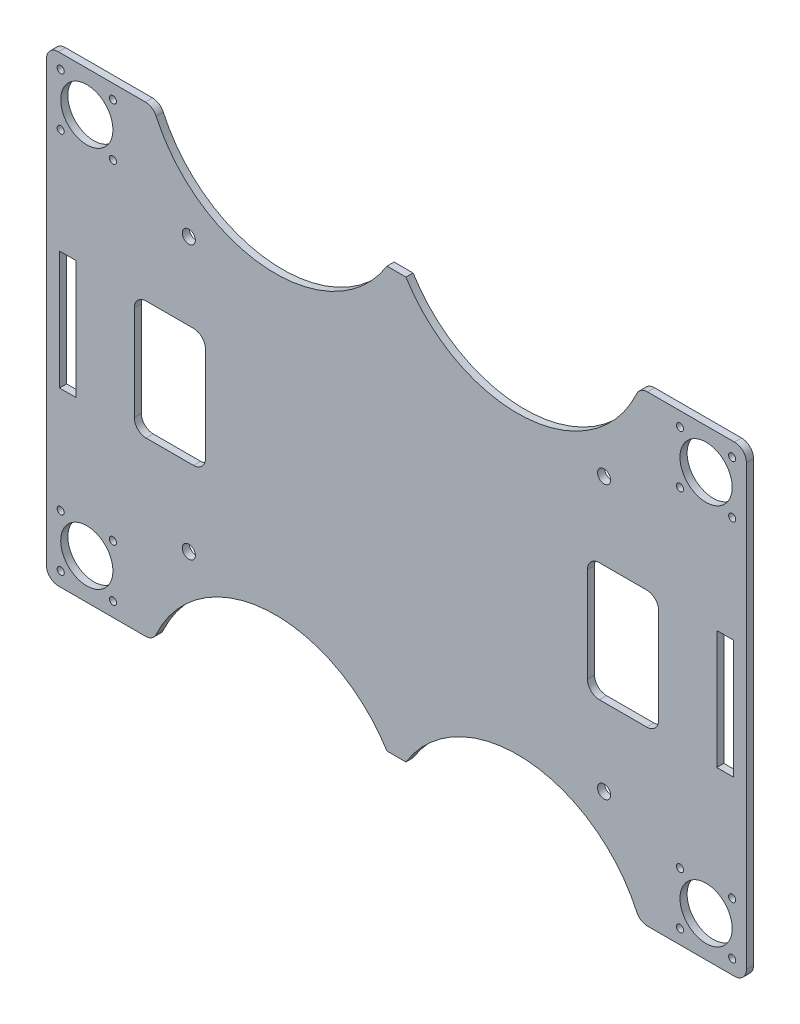
SolidWorks part; units mm, degrees
ref_plane "Plan de face" through (0, 0, 0) normal (0, 0, 1) x (1, 0, 0)
ref_plane "Plan de dessus" through (0, 0, 0) normal (0, 1, 0) x (1, 0, 0)
ref_plane "Plan de droite" through (0, 0, 0) normal (1, 0, 0) x (0, 0, -1)
sketch "Esquisse1" plane through (0, 0, 0) normal (0, 0, 1) x (1, 0, 0)
  line L0 (147.5, 48.0502) -> (147.5, -224.4935) construction
  line L1 (5, 0) -> (41.6849, 0)
  line L2 (0, -5) -> (0, -190)
  line L3 (5, -195) -> (41.6849, -195)
  line L4 (295, -5) -> (295, -190)
  line L5 (-64.1158, -97.5) -> (352.9454, -97.5) construction
  line L6 (253.3151, 0) -> (290, 0)
  line L7 (253.3151, -195) -> (290, -195)
  line L8 (151.5, -9) -> (143.5, -9)
  line L9 (151.5, -186) -> (143.5, -186)
  line L10 (-26.8235, -17) -> (37.1508, -17) construction
  line L11 (17, 13.3483) -> (17, -39.4559) construction
  line L12 (-23.9724, 20) -> (312.0368, 20) construction
  line L13 (96.4886, 48.0502) -> (96.4886, 6.2328) construction
  line L14 (198.5114, 48.0502) -> (198.5114, 6.2328) construction
  line L15 (278, 13.3483) -> (278, -39.4559) construction
  line L16 (321.8235, -17) -> (257.8492, -17) construction
  line L17 (278, -208.3483) -> (278, -155.5441) construction
  line L18 (321.8235, -178) -> (257.8492, -178) construction
  line L19 (17, -208.3483) -> (17, -155.5441) construction
  line L20 (-26.8235, -178) -> (37.1508, -178) construction
  line L21 (228, -77.5) -> (228, -117.5)
  line L22 (42, -72.5) -> (62, -72.5)
  line L23 (37, -77.5) -> (37, -117.5)
  line L24 (42, -122.5) -> (62, -122.5)
  line L25 (67, -77.5) -> (67, -117.5)
  line L26 (253, -122.5) -> (233, -122.5)
  line L27 (258, -77.5) -> (258, -117.5)
  line L28 (253, -72.5) -> (233, -72.5)
  line L29 (289.5, -122.5) -> (282.5, -122.5)
  line L30 (5.5, -72.5) -> (12.5, -72.5)
  line L31 (5.5, -72.5) -> (5.5, -122.5)
  line L32 (5.5, -122.5) -> (12.5, -122.5)
  line L33 (12.5, -72.5) -> (12.5, -122.5)
  line L34 (289.5, -72.5) -> (282.5, -72.5)
  line L35 (289.5, -72.5) -> (289.5, -122.5)
  line L36 (282.5, -72.5) -> (282.5, -122.5)
  line L37 (9, -55.2244) -> (9, -136.6659) construction
  line L38 (52, -55.2244) -> (52, -136.6659) construction
  line L39 (243, -55.2244) -> (243, -136.6659) construction
  line L40 (286, -55.2244) -> (286, -136.6659) construction
  line L41 (236.6323, -55.75) -> (56.6881, -55.75) construction
  line L42 (236.6323, -139.25) -> (56.6881, -139.25) construction
  arc A0 (143.5, -9) -> (46.234, -2.9248) centre (96.4886, 20) cw
  arc A1 (151.5, -9) -> (248.766, -2.9248) centre (198.5114, 20) ccw
  arc A2 (151.5, -186) -> (248.766, -192.0752) centre (198.5114, -215) cw
  arc A3 (143.5, -186) -> (46.234, -192.0752) centre (96.4886, -215) ccw
  circle A4 centre (60, -40) radius 2.75
  circle A5 centre (17, -17) radius 11
  circle A6 centre (6, -6) radius 1.5
  circle A7 centre (28, -6) radius 1.5
  circle A8 centre (28, -28) radius 1.5
  circle A9 centre (6, -28) radius 1.5
  circle A10 centre (235, -40) radius 2.75
  circle A11 centre (289, -6) radius 1.5
  circle A12 centre (267, -6) radius 1.5
  circle A13 centre (278, -17) radius 11
  circle A14 centre (289, -28) radius 1.5
  circle A15 centre (267, -28) radius 1.5
  circle A16 centre (267, -189) radius 1.5
  circle A17 centre (289, -189) radius 1.5
  circle A18 centre (289, -167) radius 1.5
  circle A19 centre (267, -167) radius 1.5
  circle A20 centre (278, -178) radius 11
  circle A21 centre (235, -155) radius 2.75
  circle A22 centre (60, -155) radius 2.75
  circle A23 centre (6, -189) radius 1.5
  circle A24 centre (28, -189) radius 1.5
  circle A25 centre (17, -178) radius 11
  circle A26 centre (6, -167) radius 1.5
  circle A27 centre (28, -167) radius 1.5
  arc A28 (295, -5) -> (290, 0) centre (290, -5) ccw
  arc A29 (248.766, -2.9248) -> (253.3151, 0) centre (253.3151, -5) cw
  arc A30 (46.234, -2.9248) -> (41.6849, 0) centre (41.6849, -5) ccw
  arc A31 (5, 0) -> (0, -5) centre (5, -5) ccw
  arc A32 (0, -190) -> (5, -195) centre (5, -190) ccw
  arc A33 (41.6849, -195) -> (46.234, -192.0752) centre (41.6849, -190) ccw
  arc A34 (248.766, -192.0752) -> (253.3151, -195) centre (253.3151, -190) ccw
  arc A35 (290, -195) -> (295, -190) centre (290, -190) ccw
  arc A36 (42, -72.5) -> (37, -77.5) centre (42, -77.5) ccw
  arc A37 (37, -117.5) -> (42, -122.5) centre (42, -117.5) ccw
  arc A38 (62, -122.5) -> (67, -117.5) centre (62, -117.5) ccw
  arc A39 (67, -77.5) -> (62, -72.5) centre (62, -77.5) ccw
  arc A40 (233, -72.5) -> (228, -77.5) centre (233, -77.5) ccw
  arc A41 (228, -117.5) -> (233, -122.5) centre (233, -117.5) ccw
  arc A42 (253, -122.5) -> (258, -117.5) centre (253, -117.5) ccw
  arc A43 (258, -77.5) -> (253, -72.5) centre (253, -77.5) ccw
  point P22 (147.5, -9)
  point P30 (37, -72.5)
  point P125 (295, 0)
  point P128 (250, 0)
  point P131 (45, 0)
  point P134 (0, 0)
  point P137 (0, -195)
  point P140 (45, -195)
  point P143 (250, -195)
  point P148 (37, -122.5)
  point P151 (67, -122.5)
  point P154 (67, -72.5)
  point P157 (228, -72.5)
  point P160 (228, -122.5)
  point P163 (258, -122.5)
  point P166 (258, -72.5)
  dimension "D3" = 20
  dimension "D7" = 5.5
  dimension "D10" = 22
  dimension "D13" = 3
  dimension "D18" = 30
  dimension "D24" = 5
  dimension "D25" = 5
  dimension "D26" = 5
  dimension "D27" = 5
  dimension "D28" = 5
  dimension "D29" = 5
  dimension "D30" = 5
  dimension "D31" = 5
  dimension "D32" = 5
  dimension "D1" = 295
  dimension "D2" = 195
  dimension "D4" = 45
  dimension "D5" = 4
  dimension "D6" = 9
  dimension "D8" = 60
  dimension "D9" = 40
  dimension "D11" = 17
  dimension "D12" = 17
  dimension "D14" = 11
  dimension "D15" = 11
  dimension "D17" = 50
  dimension "D16" = 51.0114
  dimension "D19" = 7
  dimension "D20" = 9
  dimension "D21" = 52
  dimension "D22" = 50
  dimension "D23" = 83.5
extrude "Boss.-Extru.1" add sketch "Esquisse1" along normal blind 3
